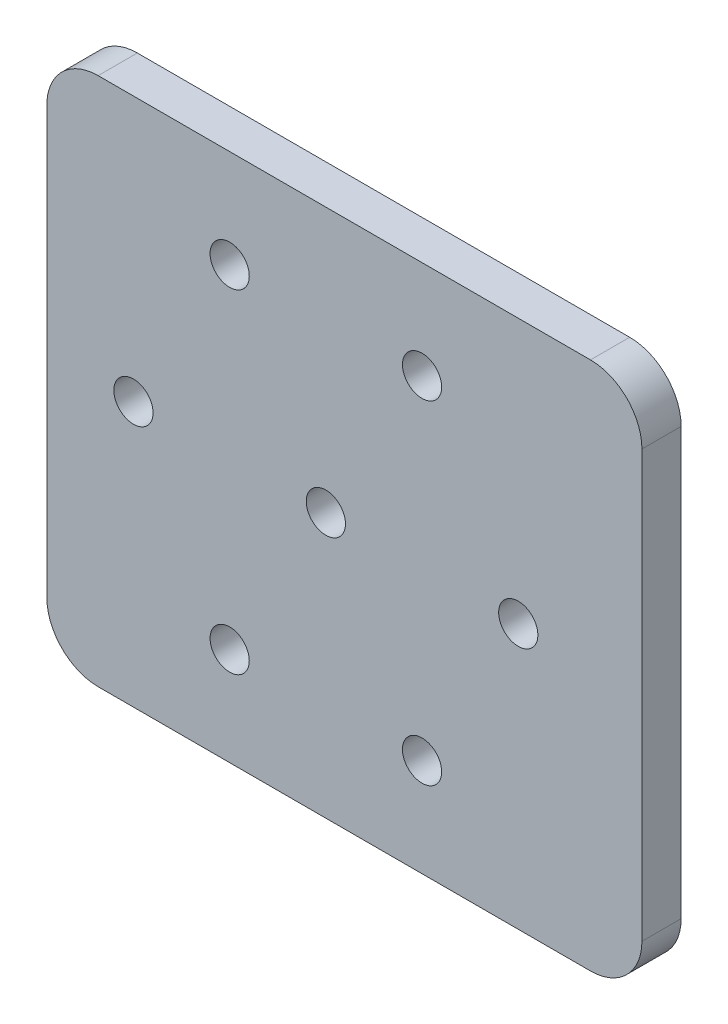
SolidWorks part; units mm, degrees
ref_plane "Front Plane" through (0, 0, 0) normal (0, 0, 1) x (1, 0, 0)
ref_plane "Top Plane" through (0, 0, 0) normal (0, 1, 0) x (1, 0, 0)
ref_plane "Right Plane" through (0, 0, 0) normal (1, 0, 0) x (0, 0, -1)
sketch "Sketch1" plane through (0, 0, 0) normal (0, 0, 1) x (1, 0, 0)
  line L1 (-196.85, -171.45) -> (196.85, -171.45)
  line L2 (-230.1875, -138.1125) -> (-230.1875, 138.1125)
  line L3 (-196.85, 171.45) -> (196.85, 171.45)
  line L4 (230.1875, -138.1125) -> (230.1875, 138.1125)
  line L5 (-230.1875, -171.45) -> (-218.9451, -163.0764) construction
  arc A0 (-196.85, 171.45) -> (-230.1875, 138.1125) centre (-196.85, 138.1125) ccw
  arc A1 (-230.1875, -138.1125) -> (-196.85, -171.45) centre (-196.85, -138.1125) ccw
  arc A2 (230.1875, 138.1125) -> (196.85, 171.45) centre (196.85, 138.1125) ccw
  arc A4 (196.85, -171.45) -> (230.1875, -138.1125) centre (196.85, -138.1125) ccw
  point P0 (0, 0)
  point P6 (0, 0)
  dimension "D1" = 33.3375
  dimension "D2" = 230.1875
  dimension "D3" = 393.7
  dimension "D4" = 276.225
  dimension "D5" = 171.45
extrude "Boss-Extrude1" add sketch "Sketch1" along normal blind 25.4
sketch "Sketch2" plane through (0, 0, 25.4) normal (0, 0, 1) x (1, 0, 0)
  line L0 (230.1875, -138.1125) -> (230.1875, 138.1125) construction
  line L1 (196.85, 171.45) -> (-196.85, 171.45) construction
  line L2 (-230.1875, 138.1125) -> (-230.1875, -138.1125)
  line L4 (-122.1374, 171.45) -> (-155.4601, 171.45)
  line L5 (-155.4601, 171.45) -> (-196.85, 171.45)
  line L6 (-155.4601, 171.45) -> (-88.8147, 171.45) construction
  line L7 (-196.85, -171.45) -> (-122.0252, -171.45)
  line L8 (-155.3627, 139.9758) -> (-155.3627, -138.1125)
  line L9 (-155.3627, 139.9758) -> (-155.3627, 104.902) construction
  line L10 (-155.3627, 104.902) -> (-88.8147, 104.902) construction
  line L11 (-88.8147, 171.45) -> (-88.8147, 104.902) construction
  line L12 (-155.4601, 171.45) -> (-88.8147, 104.902) construction
  line L13 (-196.85, -171.45) -> (196.85, -171.45) construction
  arc A0 (-196.85, 171.45) -> (-230.1875, 138.1125) centre (-196.85, 138.1125) ccw
  arc A1 (-155.3627, -138.1125) -> (-122.0252, -171.45) centre (-122.0252, -138.1125) ccw
  arc A2 (-122.1374, 171.45) -> (-155.3627, 139.9758) centre (-122.1374, 138.176) ccw
  arc A3 (-230.1875, -138.1125) -> (-196.85, -171.45) centre (-196.85, -138.1125) ccw
  point P21 (-122.1374, 138.176)
  point P27 (-122.0252, -138.1125)
  dimension "D2" = 319.0022
  dimension "D1" = 66.548
  dimension "D3" = 352.3249
extrude "Cut-Extrude1" cut sketch "Sketch2" against normal blind 25.4
hole_wizard "1 (1) Diameter Hole1" positions "Sketch5" profile "Sketch6" hole size "1" standard "ANSI Inch" end condition through all
sketch "Sketch5" plane through (0, 0, 25.4) normal (0, 0, 1) x (1, 0, 0)
  line L48 (0, 0) -> (25.4, 0) construction
  line L51 (-36.925, 107.95) -> (-99.2499, 0) construction
  line L52 (-99.2499, 0) -> (-36.925, -107.95) construction
  line L53 (-36.925, -107.95) -> (87.725, -107.95) construction
  line L54 (87.725, -107.95) -> (150.0499, 0) construction
  line L55 (150.0499, 0) -> (87.725, 107.95) construction
  line L56 (87.725, 107.95) -> (-36.925, 107.95) construction
  line L57 (196.85, 171.45) -> (-122.1374, 171.45) construction
  circle A0 centre (25.4, 0) radius 107.95 construction
  point P170 (-36.925, 107.95)
  point P173 (87.725, 107.95)
  point P176 (150.0499, 0)
  point P179 (87.725, -107.95)
  point P182 (-36.925, -107.95)
  point P185 (-99.2499, 0)
  point P188 (25.4, 0)
  dimension "D1" = 25.4
  dimension "D2" = 215.9
sketch "Sketch6" plane through (25.4, 0, 25.4) normal (1, 0, 0) x (0, -1, 0)
  line L0 (0, 0) -> (0, 25.4)
  line L1 (0, 25.4) -> (12.7, 25.4)
  line L2 (12.7, 25.4) -> (12.7, 0)
  line L5 (12.7, 0) -> (0, 0)
  line L11 (0, -6.35) -> (0, 107.95) construction
  dimension "Thru Hole Dia." = 25.4
  dimension "Thru Hole Depth" = 25.4
